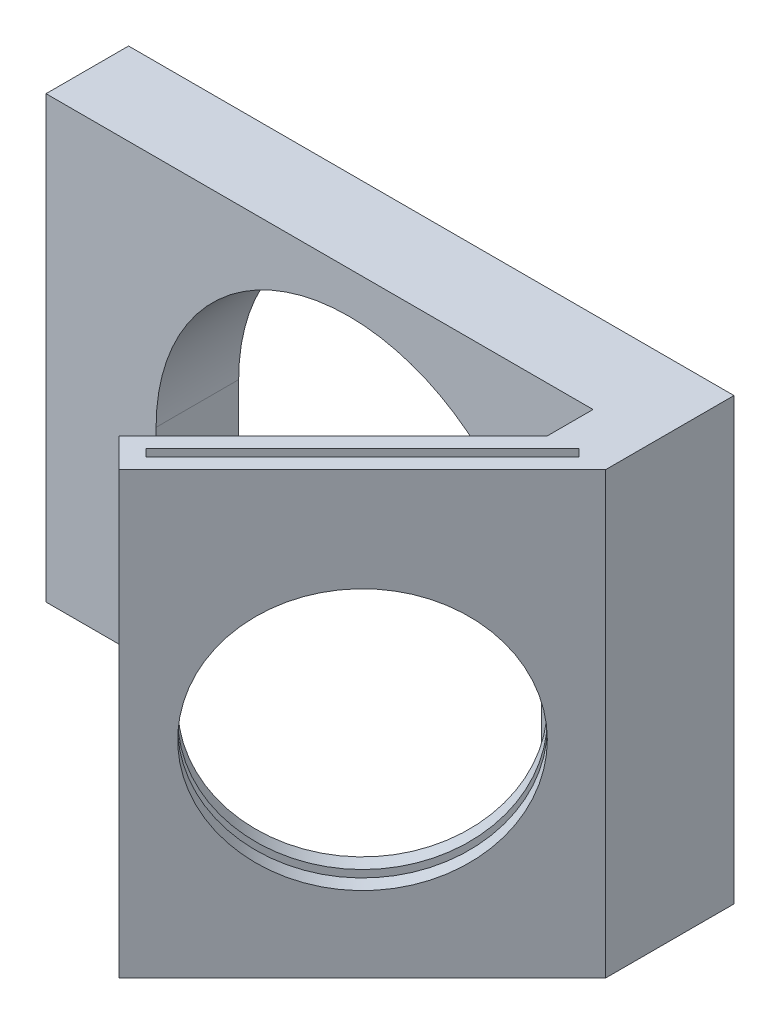
SolidWorks part; units mm, degrees
ref_plane "Alzado" through (0, 0, 0) normal (0, 0, 1) x (1, 0, 0)
ref_plane "Planta" through (0, 0, 0) normal (0, 1, 0) x (1, 0, 0)
ref_plane "Vista lateral" through (0, 0, 0) normal (1, 0, 0) x (0, 0, -1)
sketch "Croquis1" plane through (0, 0, 0) normal (0, 0, 1) x (1, 0, 0)
  line L0 (-22, 17) -> (-22, -15)
  line L1 (-22, -15) -> (-14, -15)
  line L2 (22, -15) -> (22, 17)
  line L3 (14, -15) -> (22, -15)
  line L4 (14, 0) -> (14, -15)
  line L5 (-22, 17) -> (22, 17)
  line L6 (-14, 0) -> (-14, -15)
  line L7 (-22.9427, 14) -> (27.3205, 14) construction
  arc A0 (14, 0) -> (-14, 0) centre (0, 0) ccw
  dimension "D2" = 28
  dimension "D3" = 15
  dimension "D1" = 3
  dimension "D4" = 8
extrude "Saliente-Extruir1" add sketch "Croquis1" along normal blind 6
sketch "Croquis2" plane through (0, -15, 0) normal (0, -1, 0) x (1, 0, 0)
  line L0 (22, 6) -> (22, 9.3223)
  line L1 (22, 9.3223) -> (4.3223, 27)
  line L2 (0, 5) -> (0, 66.8344) construction
  line L3 (0, 5) -> (36.4427, 41.4427) construction
  line L4 (0, 5) -> (-39.2518, 44.2518) construction
  line L5 (4.3223, 27) -> (0, 5) construction
  line L6 (0, 5) -> (22, 9.3223) construction
  line L7 (22, 6) -> (17.7574, 6)
  line L8 (17.7574, 6) -> (17.7574, 9.3223)
  line L9 (17.7574, 9.3223) -> (2.201, 24.8787)
  line L10 (2.201, 24.8787) -> (4.3223, 27)
  dimension "D1" = 45
  dimension "D2" = 45
  dimension "D3" = 5
  dimension "D4" = 25
  dimension "D5" = 3
extrude "Saliente-Extruir2" add sketch "Croquis2" against normal up to vertex (32 mm away)
sketch "Croquis3" plane through (15.6612, 0, 15.6612) normal (0.7071, 0, 0.7071) x (0.7071, 0, -0.7071)
  line L0 (-3.5355, -15) -> (-3.5355, 17) construction
  line L1 (8.9645, -15) -> (-16.0355, -15) construction
  line L2 (8.9645, 17) -> (-16.0355, 17) construction
  circle A0 centre (-3.5355, 0) radius 9.5
  dimension "D2" = 19
  dimension "D1" = 17
extrude "Cortar-Extruir1" cut sketch "Croquis3" against normal up to next
sketch "Croquis4" plane through (15.6612, 0, 15.6612) normal (0.7071, 0, 0.7071) x (0.7071, 0, -0.7071)
  line L0 (-13.0355, 0) -> (5.9645, 0) construction
  line L2 (-3.5355, 9.5) -> (-3.5355, -9.5) construction
  circle A0 centre (-3.5355, 0) radius 9.5 construction
sketch "Croquis5" plane through (0, 17, 0) normal (0, 1, 0) x (1, 0, 0)
  line L0 (4.4991, -25.2322) -> (20.2322, -9.4991)
  line L1 (20.2322, -9.4991) -> (19.7019, -8.9688)
  line L2 (19.7019, -8.9688) -> (3.9688, -24.7019)
  line L3 (22, -9.3223) -> (4.3223, -27) construction
  line L4 (3.9688, -24.7019) -> (4.4991, -25.2322)
  line L5 (4.2339, -24.9671) -> (3.2617, -25.9393) construction
  line L6 (2.201, -24.8787) -> (4.3223, -27) construction
  line L7 (12.3657, -17.3657) -> (13.1612, -18.1612) construction
  line L8 (22, -9.3223) -> (4.3223, -27) construction
  line L9 (4.3223, -27) -> (2.201, -24.8787) construction
  dimension "D1" = 0.75
  dimension "D2" = 22.25
extrude "Cortar-Extruir2" cut sketch "Croquis5" against normal blind 31
